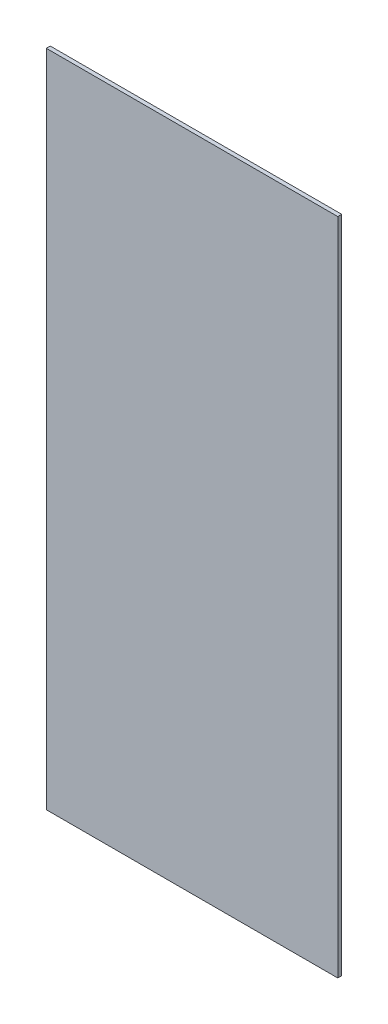
SolidWorks part; units mm, degrees
material "Plain Carbon Steel"
ref_plane "Front Plane" through (0, 0, 0) normal (0, 0, 1) x (1, 0, 0)
ref_plane "Top Plane" through (0, 0, 0) normal (0, 1, 0) x (1, 0, 0)
ref_plane "Right Plane" through (0, 0, 0) normal (1, 0, 0) x (0, 0, -1)
sketch "Sketch1" plane through (0, 0, 0) normal (0, 0, 1) x (1, 0, 0)
  line L1 (0, 0) -> (112.268, 0)
  line L2 (0, 0) -> (0, 254)
  line L3 (0, 254) -> (112.268, 254)
  line L4 (112.268, 0) -> (112.268, 254)
  dimension "D1" = 254
  dimension "D2" = 112.268
extrude "Bottom Outer Casing" add sketch "Sketch1" along normal blind 1.5189
